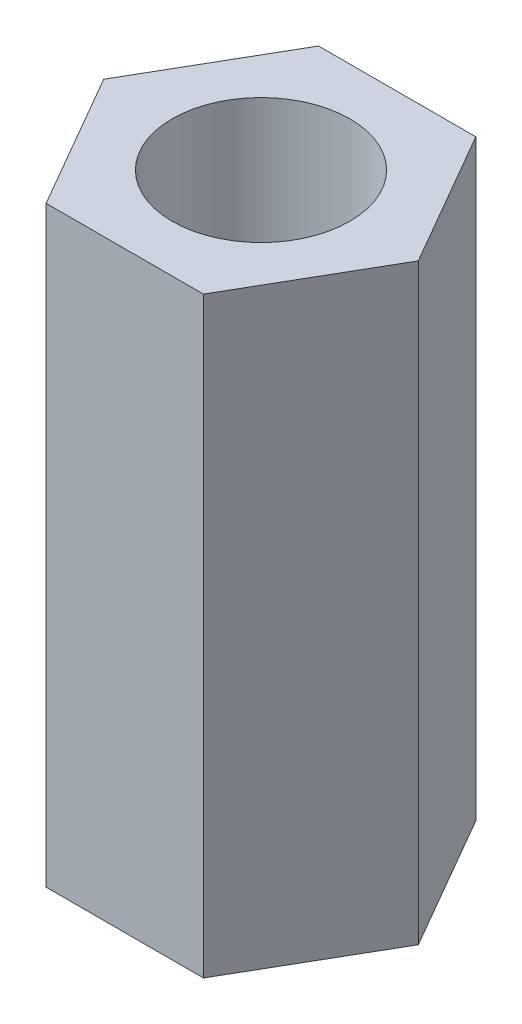
SolidWorks part; units mm, degrees
ref_plane "前视基准面" through (0, 0, 0) normal (0, 0, 1) x (1, 0, 0)
ref_plane "上视基准面" through (0, 0, 0) normal (0, 1, 0) x (1, 0, 0)
ref_plane "右视基准面" through (0, 0, 0) normal (1, 0, 0) x (0, 0, -1)
sketch "草图1" plane through (0, 0, 0) normal (0, 1, 0) x (1, 0, 0)
  line L1 (-1.3279, 2.3) -> (-2.6558, 0)
  line L2 (-2.6558, 0) -> (-1.3279, -2.3)
  line L3 (-1.3279, -2.3) -> (1.3279, -2.3)
  line L4 (1.3279, -2.3) -> (2.6558, 0)
  line L5 (2.6558, 0) -> (1.3279, 2.3)
  line L6 (1.3279, 2.3) -> (-1.3279, 2.3)
  circle A0 centre (0, 0) radius 2.3
  circle A1 centre (0, 0) radius 2.3 construction
  circle A2 centre (0, 0) radius 1.5
  dimension "D1" = 4.6
  dimension "D4" = 3
  dimension "D2" = 4.6
  dimension "D3" = 5.3116
extrude "凸台-拉伸2" add sketch "草图1" along normal blind 5 contours A0 A2 | A0 L6 L1 | A0 L1 L2 | A0 L5 L6 | A0 L4 L5 | A0 L3 L4 | A0 L2 L3
sketch "Sketch1" plane through (0, 5, 0) normal (0, 1, 0) x (1, 0, 0)
  line L1 (1.3279, 2.3) -> (-1.3279, 2.3)
  line L2 (-1.3279, 2.3) -> (-2.6558, 0)
  line L3 (-2.6558, 0) -> (-1.3279, -2.3)
  line L4 (-1.3279, -2.3) -> (1.3279, -2.3)
  line L5 (1.3279, -2.3) -> (2.6558, 0)
  line L6 (2.6558, 0) -> (1.3279, 2.3)
  circle A0 centre (0, 0) radius 1.5
  circle A1 centre (0, 0) radius 2.3 construction
extrude "Boss-Extrude1" add sketch "Sketch1" along normal blind 5
